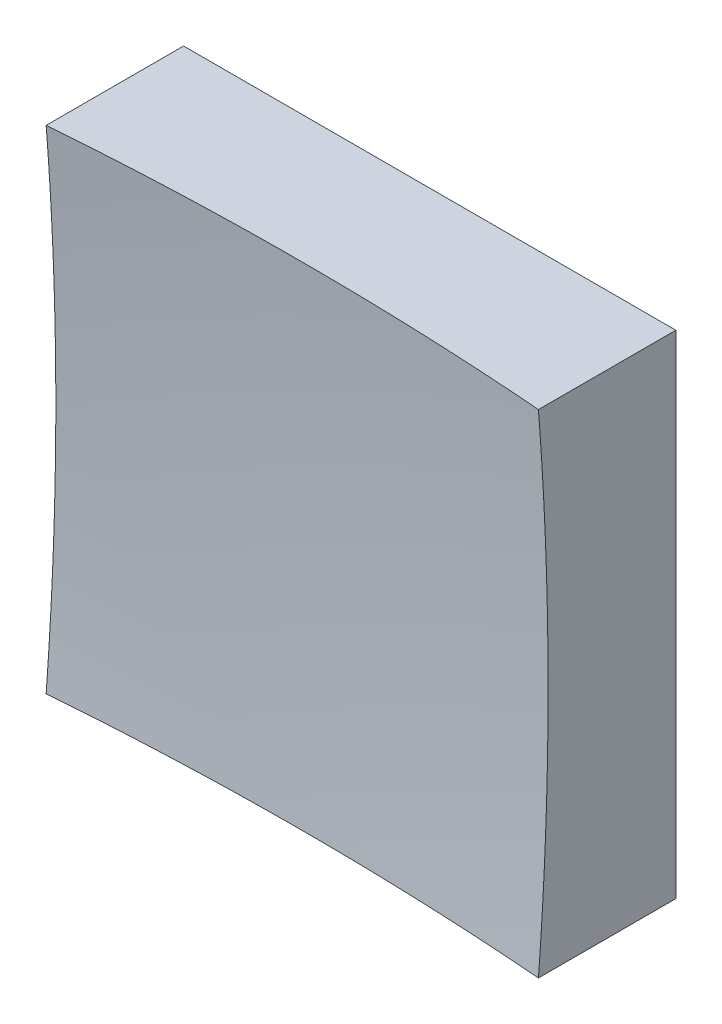
SolidWorks part; units mm, degrees
ref_plane "前视基准面" through (0, 0, 0) normal (0, 0, 1) x (1, 0, 0)
ref_plane "上视基准面" through (0, 0, 0) normal (0, 1, 0) x (1, 0, 0)
ref_plane "右视基准面" through (0, 0, 0) normal (1, 0, 0) x (0, 0, -1)
sketch "草图1" plane through (0, 0, 0) normal (0, 0, 1) x (1, 0, 0)
  line L1 (-6.25, 6.25) -> (6.25, 6.25)
  line L2 (-6.25, 6.25) -> (-6.25, -6.25)
  line L3 (-6.25, -6.25) -> (6.25, -6.25)
  line L4 (6.25, 6.25) -> (6.25, -6.25)
  line L5 (-6.25, 6.25) -> (6.25, -6.25) construction
  line L6 (-6.25, -6.25) -> (6.25, 6.25) construction
  point P0 (0, 0)
  dimension "D1" = 12.5
  dimension "D2" = 12.5
extrude "凸台-拉伸1" add sketch "草图1" along normal blind 10 contours L2 L3 L4 L1
sketch "草图2" plane through (0, 0, 0) normal (0, 1, 0) x (1, 0, 0)
  line L0 (-7.4603, -3) -> (7.3192, -3) construction
  line L1 (0, 0) -> (0, -12.1749) construction
  line L2 (77.9876, -65.1695) -> (0, -65.1695)
  line L3 (0, -65.1695) -> (0, -3)
  arc A1 (77.9876, -65.1695) -> (0, -3) centre (0, -83) ccw
  dimension "D2" = 160
  dimension "D1" = 3
revolve "切除-旋转2" cut sketch "草图2" angle 360 about L3
